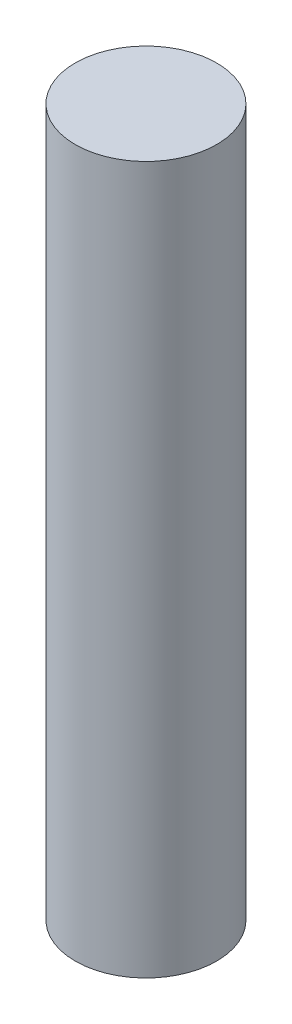
SolidWorks part; units mm, degrees
ref_plane "Front Plane" through (0, 0, 0) normal (0, 0, 1) x (1, 0, 0)
ref_plane "Top Plane" through (0, 0, 0) normal (0, 1, 0) x (1, 0, 0)
ref_plane "Right Plane" through (0, 0, 0) normal (1, 0, 0) x (0, 0, -1)
sketch "Sketch1" plane through (0, 0, 0) normal (0, 1, 0) x (1, 0, 0)
  circle A0 centre (0, 0) radius 1.5
  dimension "D1" = 3
extrude "Boss-Extrude1" add sketch "Sketch1" along normal blind 15
